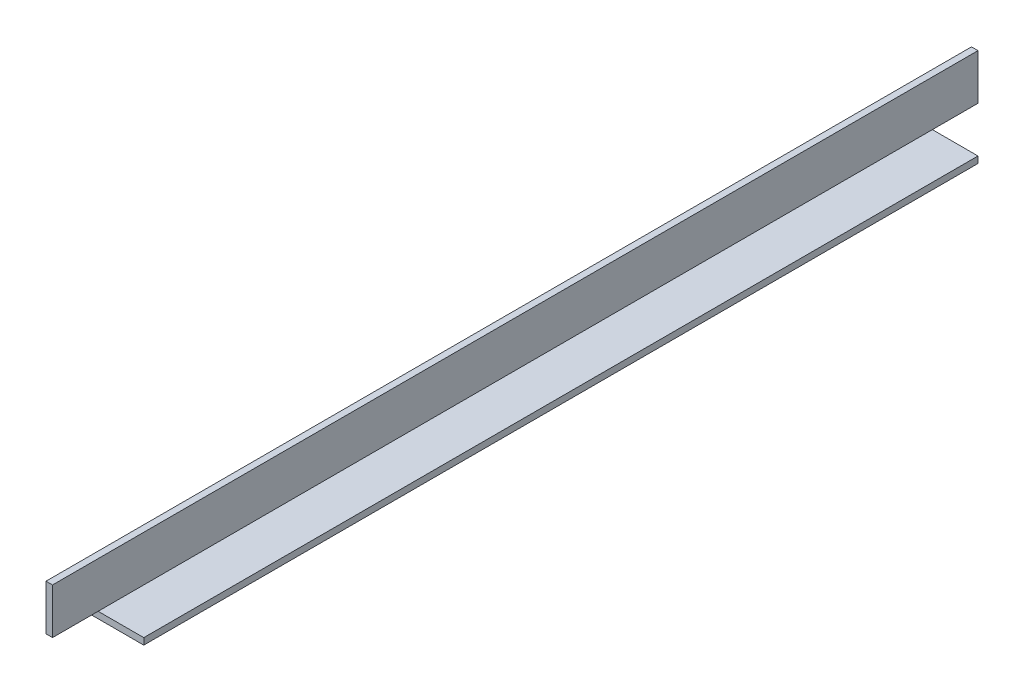
SolidWorks part; units mm, degrees
ref_plane "Front Plane" through (0, 0, 0) normal (0, 0, 1) x (1, 0, 0)
ref_plane "Top Plane" through (0, 0, 0) normal (0, 1, 0) x (1, 0, 0)
ref_plane "Right Plane" through (0, 0, 0) normal (1, 0, 0) x (0, 0, -1)
sketch "Sketch1" plane through (0, 0, 0) normal (0, 0, 1) x (1, 0, 0)
  line L0 (0, 0) -> (0, 25.4)
  line L1 (0, -55) -> (0, 55) construction
  line L2 (0, 25.4) -> (3.175, 25.4)
  line L3 (3.175, 25.4) -> (3.175, 3.175)
  line L4 (3.175, 3.175) -> (25.4, 3.175)
  line L5 (25.4, 3.175) -> (25.4, 0)
  line L6 (55, 0) -> (-55, 0) construction
  line L7 (25.4, 0) -> (0, 0)
  dimension "D1" = 25.4
  dimension "D2" = 25.4
  dimension "D3" = 3.175
  dimension "D4" = 3.175
extrude "Boss-Extrude1" add sketch "Sketch1" along normal blind 450.85
sketch "Sketch2" plane through (25.4, 0, 0) normal (1, 0, 0) x (0, 0, -1)
  line L0 (-450.85, 3.175) -> (-428.625, 3.175)
  line L1 (-450.85, 3.175) -> (0, 3.175) construction
  line L2 (-428.625, 3.175) -> (-428.625, 0)
  line L3 (13.97, 0) -> (-13.97, 0) construction
  line L4 (-428.625, 0) -> (-450.85, 0)
  line L5 (-450.85, 0) -> (-450.85, 3.175) construction
  line L6 (-450.85, 0) -> (-450.85, 3.175)
  line L7 (0, 3.175) -> (-22.225, 3.175)
  line L8 (0, 13.97) -> (0, -13.97) construction
  line L9 (-450.85, 3.175) -> (0, 3.175) construction
  line L10 (-22.225, 3.175) -> (-22.225, 0)
  line L11 (-22.225, 0) -> (0, 0)
  line L12 (0, 0) -> (0, 3.175)
  dimension "D1" = 22.225
  dimension "D2" = 22.225
  dimension "D3" = 90
extrude "Cut-Extrude1" cut sketch "Sketch2" against normal through all
